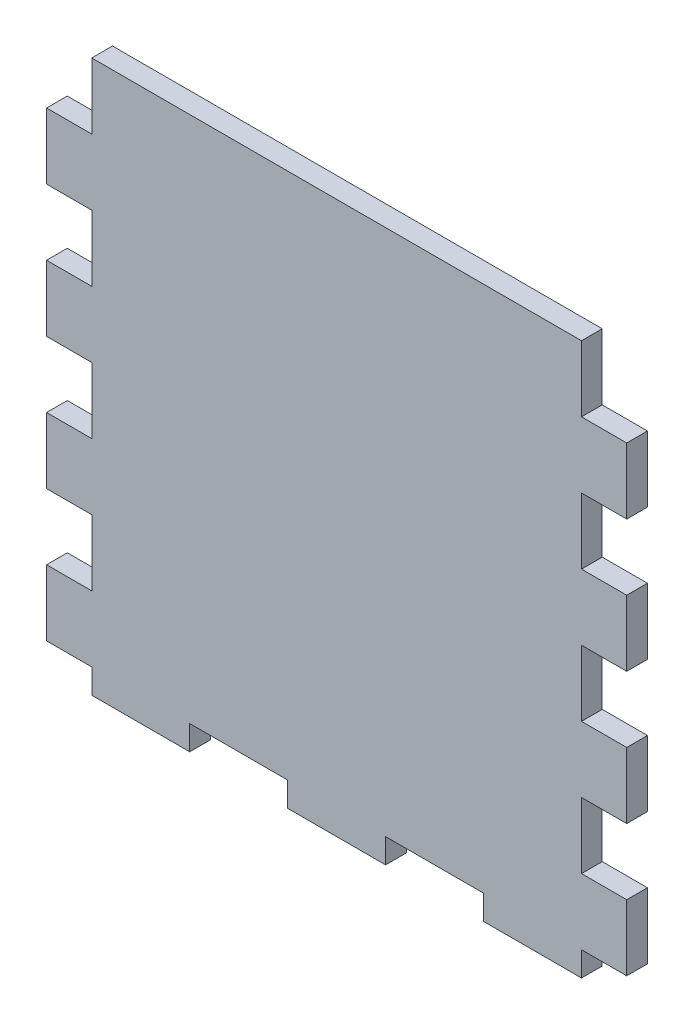
SolidWorks part; units mm, degrees
ref_plane "Front Plane" through (0, 0, 0) normal (0, 0, 1) x (1, 0, 0)
ref_plane "Top Plane" through (0, 0, 0) normal (0, 1, 0) x (1, 0, 0)
ref_plane "Right Plane" through (0, 0, 0) normal (1, 0, 0) x (0, 0, -1)
sketch "Sketch1" plane through (0, 0, 0) normal (0, 0, 1) x (1, 0, 0)
  line L1 (0, 0) -> (65, 0)
  line L2 (0, 0) -> (0, 70)
  line L3 (0, 70) -> (65, 70)
  line L4 (65, 0) -> (65, 70)
  dimension "D1" = 65
  dimension "D2" = 70
extrude "Boss-Extrude1" add sketch "Sketch1" along normal blind 2.75
sketch "Sketch2" plane through (0, 0, 2.75) normal (0, 0, 1) x (1, 0, 0)
  line L0 (-6, 8.75) -> (-6, 17.5) construction
  line L1 (0, 0) -> (-6, 0)
  line L2 (0, 0) -> (0, 8.75)
  line L3 (0, 8.75) -> (-6, 8.75)
  line L4 (-6, 0) -> (-6, 8.75)
  line L5 (0, 17.5) -> (-6, 17.5)
  line L6 (0, 17.5) -> (0, 26.25)
  line L7 (0, 26.25) -> (-6, 26.25)
  line L8 (-6, 17.5) -> (-6, 26.25)
  line L9 (-6, 26.25) -> (-6, 35) construction
  line L10 (0, 35) -> (-6, 35)
  line L11 (0, 35) -> (0, 43.75)
  line L12 (0, 43.75) -> (-6, 43.75)
  line L13 (-6, 35) -> (-6, 43.75)
  line L14 (-6, 43.75) -> (-6, 52.5) construction
  line L15 (0, 52.5) -> (-6, 52.5)
  line L16 (0, 52.5) -> (0, 61.25)
  line L17 (0, 61.25) -> (-6, 61.25)
  line L18 (-6, 52.5) -> (-6, 61.25)
  line L19 (-6, 61.25) -> (-6, 70) construction
  line L20 (65, 70) -> (0, 70) construction
  line L21 (32.5, 0) -> (32.5, 70) construction
  line L22 (0, 0) -> (65, 0) construction
  line L23 (71, 61.25) -> (71, 70) construction
  line L24 (71, 43.75) -> (71, 52.5) construction
  line L25 (71, 26.25) -> (71, 35) construction
  line L26 (71, 8.75) -> (71, 17.5) construction
  line L27 (71, 52.5) -> (71, 61.25)
  line L28 (65, 61.25) -> (71, 61.25)
  line L29 (65, 52.5) -> (65, 61.25)
  line L30 (65, 52.5) -> (71, 52.5)
  line L31 (71, 35) -> (71, 43.75)
  line L32 (65, 43.75) -> (71, 43.75)
  line L33 (65, 35) -> (65, 43.75)
  line L34 (65, 35) -> (71, 35)
  line L35 (71, 17.5) -> (71, 26.25)
  line L36 (65, 26.25) -> (71, 26.25)
  line L37 (65, 17.5) -> (65, 26.25)
  line L38 (65, 17.5) -> (71, 17.5)
  line L39 (71, 0) -> (71, 8.75)
  line L40 (65, 8.75) -> (71, 8.75)
  line L41 (65, 0) -> (65, 8.75)
  line L42 (65, 0) -> (71, 0)
  line L43 (13, -3.25) -> (26, -3.25) construction
  line L44 (0, 0) -> (13, 0)
  line L45 (0, 0) -> (0, -3.25)
  line L46 (0, -3.25) -> (13, -3.25)
  line L47 (13, 0) -> (13, -3.25)
  line L48 (26, 0) -> (26, -3.25)
  line L49 (26, -3.25) -> (39, -3.25)
  line L50 (39, 0) -> (39, -3.25)
  line L51 (39, -3.25) -> (52, -3.25) construction
  line L52 (26, 0) -> (39, 0)
  line L53 (52, 0) -> (52, -3.25)
  line L54 (52, -3.25) -> (65, -3.25)
  line L55 (65, 0) -> (65, -3.25)
  line L56 (65, -3.25) -> (78, -3.25) construction
  line L57 (52, 0) -> (65, 0)
  point P45 (20.4226, -3.0838)
  point P46 (65, -2.7473)
  point P55 (0, -2.9471)
  point P57 (62.0279, -3.9852)
  point P58 (65.4146, 0)
  line M26 (0, 70) -> (0, 0)
  line M27 (0, 0) -> (65, 0)
  line M28 (65, 0) -> (65, 70)
  dimension "D2" = 6
  dimension "D4" = 3.25
  dimension "D1" = 4
  dimension "D3" = 3
extrude "Boss-Extrude2" add sketch "Sketch2" against normal up to surface (2.75 mm away) contours L34 L31 L32 M28 | L38 L35 L36 M28 | L42 L39 L40 M28 | L47 L45 L46 M27 | L4 L1 L3 M26 | L8 L5 L7 M26 | L18 L15 L17 M26 | L29 L28 L27 L30 | L57 L53 L54 L55 | L49 L50 L52 L48 | L13 L12 L11 L10 up to face at (32.5, 35, 0)
equation "\"veneer_thickness\"= 0.5mm"
equation "\"thick\"= 2.75mm"
equation "\"D1@Boss-Extrude1\"=\"thick\""
equation "\"D2@Sketch2\"=\"thick\"*2 + \"veneer_thickness\""
equation "\"D4@Sketch2\"=\"thick\" + \"veneer_thickness\""
